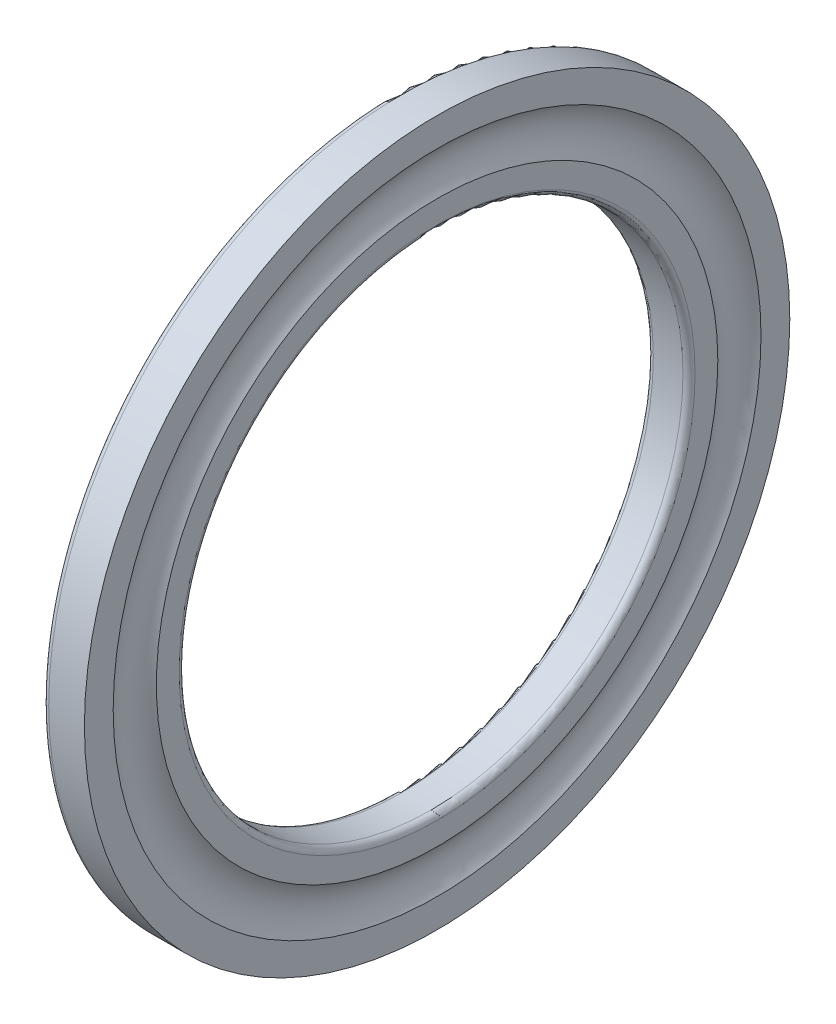
SolidWorks part; units mm, degrees
ref_plane "Alzado" through (0, 0, 0) normal (0, 0, 1) x (1, 0, 0)
ref_plane "Planta" through (0, 0, 0) normal (0, 1, 0) x (1, 0, 0)
ref_plane "Vista lateral" through (0, 0, 0) normal (1, 0, 0) x (0, 0, -1)
ref_plane "Plano1" through (0, 0, 0) normal (0, 0, 1) x (1, 0, 0)
sketch "Croquis1" plane through (0, 0, 0) normal (0, 0, 1) x (1, 0, 0)
  line L0 (0.6, 25) -> (3.542, 25)
  line L1 (4.142, 25.6) -> (4.142, 27.8573)
  line L2 (4.142, 32.1427) -> (4.142, 35)
  line L3 (4.142, 35) -> (0.6, 35)
  line L4 (0, 34.4) -> (0, 25.6)
  line L5 (3.542, 0) -> (0.6, 0) construction
  arc A0 (0, 25.6) -> (0.6, 25) centre (0.6, 25.6) ccw
  arc A1 (3.542, 25) -> (4.142, 25.6) centre (3.542, 25.6) ccw
  arc A2 (4.142, 27.8573) -> (4.142, 32.1427) centre (7, 30) cw
  arc A3 (0.6, 35) -> (0, 34.4) centre (0.6, 34.4) ccw
revolve "Revolución1" add sketch "Croquis1" angle 360 about L5
